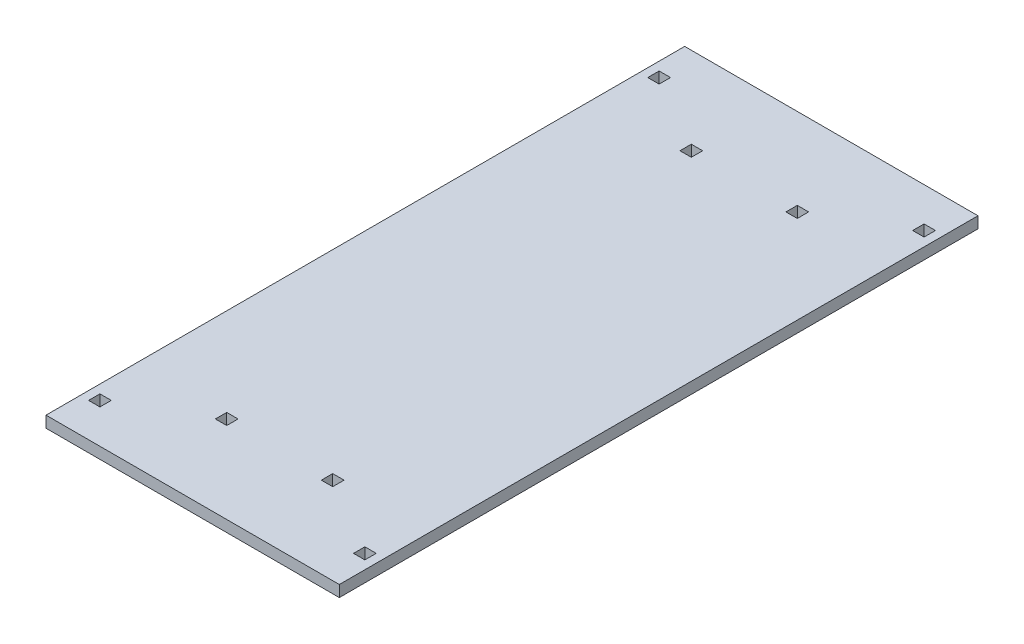
SolidWorks part; units mm, degrees
ref_plane "Front Plane" through (0, 0, 0) normal (0, 0, 1) x (1, 0, 0)
ref_plane "Top Plane" through (0, 0, 0) normal (0, 1, 0) x (1, 0, 0)
ref_plane "Right Plane" through (0, 0, 0) normal (1, 0, 0) x (0, 0, -1)
sketch "Sketch1" plane through (0, 0, 0) normal (0, 1, 0) x (1, 0, 0)
  line L0 (150, -332.5) -> (150, 332.5)
  line L1 (130, -312.5) -> (-130, -312.5)
  line L2 (130, -312.5) -> (130, 312.5)
  line L3 (130, 312.5) -> (-130, 312.5)
  line L4 (-130, -312.5) -> (-130, 312.5)
  line L5 (130, -312.5) -> (-130, 312.5) construction
  line L6 (130, 312.5) -> (-130, -312.5) construction
  line L7 (150, 332.5) -> (-150, 332.5)
  line L8 (-150, -332.5) -> (-150, 332.5)
  line L9 (150, -332.5) -> (-150, -332.5)
  line L10 (155, -337.5) -> (155, 337.5)
  line L11 (155, 337.5) -> (-155, 337.5)
  line L12 (-155, -337.5) -> (-155, 337.5)
  line L13 (155, -337.5) -> (-155, -337.5)
  point P0 (0, 0)
  dimension "D1" = 625
  dimension "D2" = 260
  dimension "D3" = 20
  dimension "D4" = 5
extrude "Boss-Extrude1" add sketch "Sketch1" along normal blind 12 contours L13 L10 L11 L12 L0 L9 L8 L7 | L9 L0 L7 L8 L1 L4 L3 L2 | L4 L1 L2 L3
sketch "Sketch2" plane through (0, 12, 0) normal (0, 1, 0) x (1, 0, 0)
  line L0 (-134, -301.5) -> (-146, -301.5)
  line L1 (-134, -301.5) -> (-134, -289.5)
  line L2 (-134, -289.5) -> (-146, -289.5)
  line L3 (-146, -301.5) -> (-146, -289.5)
  line L4 (-134, -301.5) -> (-146, -289.5) construction
  line L5 (-134, -289.5) -> (-146, -301.5) construction
  line L6 (-146, 301.5) -> (-134, 301.5)
  line L7 (-146, 301.5) -> (-146, 289.5)
  line L8 (-146, 289.5) -> (-134, 289.5)
  line L9 (-134, 301.5) -> (-134, 289.5)
  line L10 (134, 301.5) -> (146, 301.5)
  line L11 (134, 301.5) -> (134, 289.5)
  line L12 (134, 289.5) -> (146, 289.5)
  line L13 (146, 301.5) -> (146, 289.5)
  line L14 (134, -289.5) -> (146, -289.5)
  line L15 (134, -289.5) -> (134, -301.5)
  line L16 (134, -301.5) -> (146, -301.5)
  line L17 (146, -289.5) -> (146, -301.5)
  line L30 (-150, -332.5) -> (-150, 332.5) construction
  line L31 (150, -332.5) -> (-150, -332.5) construction
  line L32 (150, -332.5) -> (150, 332.5) construction
  line L33 (150, 332.5) -> (-150, 332.5) construction
  point P0 (-140, -295.5)
  dimension "D1" = 12
  dimension "D2" = 12
  dimension "D3" = 12
  dimension "D4" = 12
  dimension "D5" = 4
  dimension "D6" = 31
  dimension "D7" = 4
  dimension "D8" = 31
  dimension "D9" = 4
extrude "Cut-Extrude1" cut sketch "Sketch2" against normal through all
sketch "Sketch3" plane through (0, 12, 0) normal (0, 1, 0) x (1, 0, 0)
  line L1 (-62, -251.5) -> (-50, -251.5)
  line L2 (-62, -251.5) -> (-62, -239.5)
  line L3 (-62, -239.5) -> (-50, -239.5)
  line L4 (-50, -251.5) -> (-50, -239.5)
  line L5 (50, -251.5) -> (62, -251.5)
  line L6 (50, -251.5) -> (50, -239.5)
  line L7 (50, -239.5) -> (62, -239.5)
  line L8 (62, -251.5) -> (62, -239.5)
  line L9 (-134, -289.5) -> (-146, -289.5) construction
  line L14 (-150, -332.5) -> (-150, 332.5) construction
  dimension "D1" = 12
  dimension "D2" = 50
  dimension "12" = 12
  dimension "D3" = 100
  dimension "D4" = 88
extrude "Cut-Extrude2" cut sketch "Sketch3" against normal through all
mirror "Mirror1" about plane through (0, 0, 0) normal (0, 0, 1) of "Cut-Extrude2"
